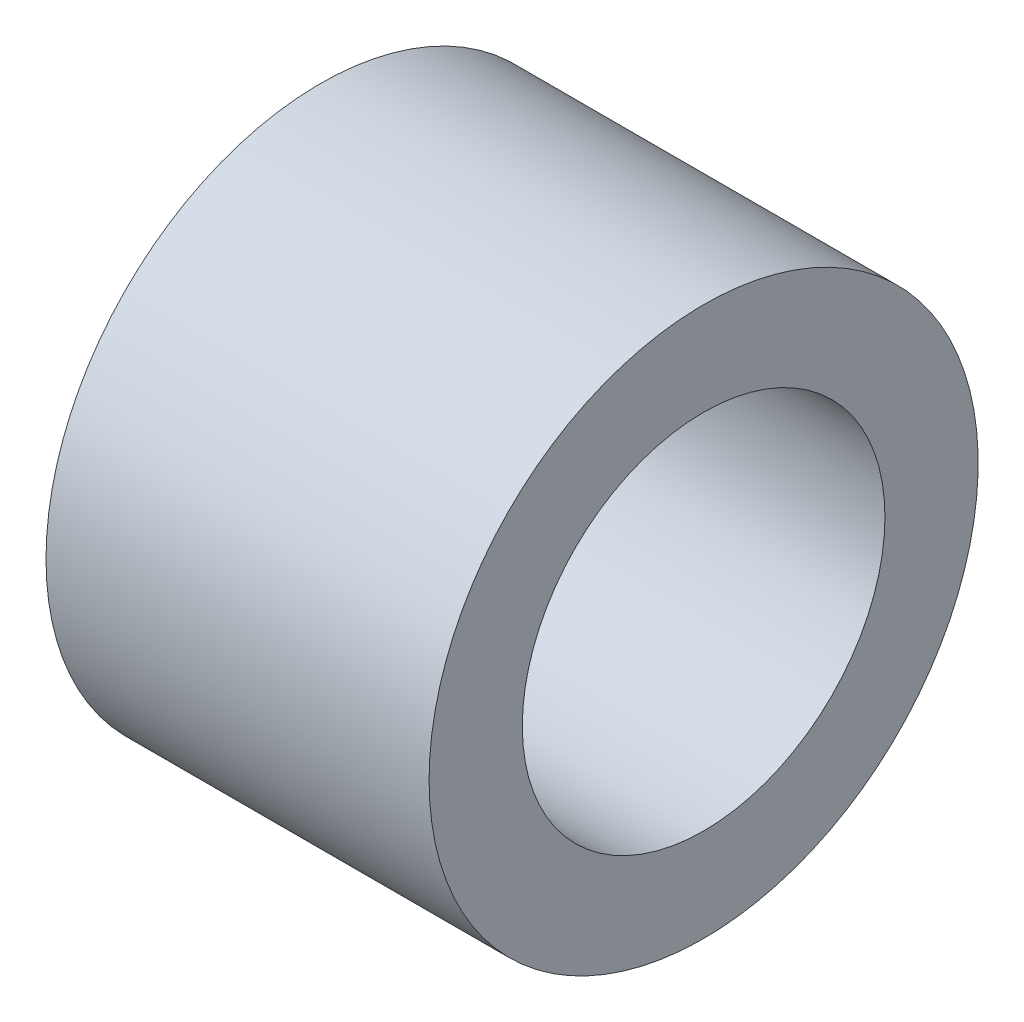
SolidWorks part; units mm, degrees
ref_plane "Face" through (0, 0, 0) normal (0, 0, 1) x (1, 0, 0)
ref_plane "Dessus" through (0, 0, 0) normal (0, 1, 0) x (1, 0, 0)
ref_plane "Droite" through (0, 0, 0) normal (1, 0, 0) x (0, 0, -1)
sketch "Esquisse1" plane through (0, 0, 0) normal (0, 0, 1) x (1, 0, 0)
  line L0 (-32.8367, 0) -> (48.3909, 0) construction
  line L1 (-14.114, 10.75) -> (0.886, 10.75)
  line L2 (0.886, 10.75) -> (0.886, 7.1)
  line L3 (0.886, 7.1) -> (-14.114, 7.1)
  line L4 (-14.114, 7.1) -> (-14.114, 10.75)
revolve "Révolution1" add sketch "Esquisse1" angle 360 about L0
